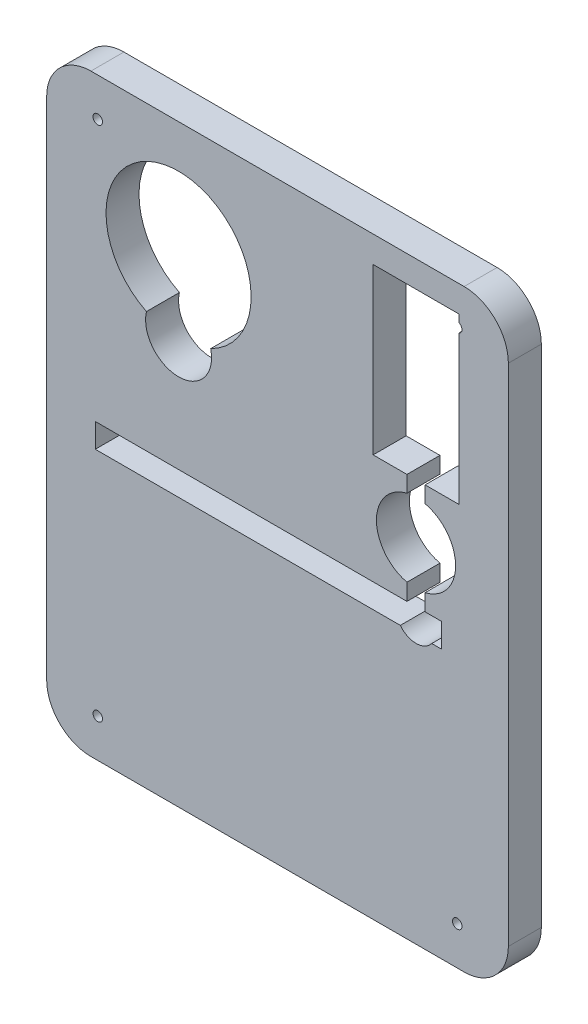
SolidWorks part; units mm, degrees
material "Polyurethane Foam Flexible"
ref_plane "Front Plane" through (0, 0, 0) normal (1, 0, 0) x (0, 1, 0)
ref_plane "Top Plane" through (0, 0, 0) normal (0, 0, 1) x (0, 1, 0)
ref_plane "Right Plane" through (0, 0, 0) normal (0, 1, 0) x (-1, 0, 0)
sketch "Sketch1" plane through (0, 0, 0) normal (0, 0, 1) x (0, 1, 0)
  line L5 (-97.2566, -88.9) -> (97.2566, -88.9)
  line L6 (-114.3, -71.8566) -> (-114.3, 71.8566)
  line L7 (-97.2566, 88.9) -> (97.2566, 88.9)
  line L8 (114.3, -71.8566) -> (114.3, 71.8566)
  arc A0 (-114.3, 71.8566) -> (-97.2566, 88.9) centre (-97.2566, 71.8566) cw
  arc A1 (-97.2566, -88.9) -> (-114.3, -71.8566) centre (-97.2566, -71.8566) cw
  arc A2 (97.2566, -88.9) -> (114.3, -71.8566) centre (97.2566, -71.8566) ccw
  arc A3 (97.2566, 88.9) -> (114.3, 71.8566) centre (97.2566, 71.8566) cw
  point P15 (114.3, 0)
  point P20 (0, 88.9)
  dimension "D1" = 17.0434
  dimension "D2" = 177.8
  dimension "D3" = 228.6
extrude "Boss-Extrude1" add sketch "Sketch1" along normal blind 12.7
sketch "Sketch2" plane through (0, 0, 12.7) normal (0, 0, 1) x (1, 0, 0)
  line L0 (0, 223.1681) -> (0, -217.0396) construction
  line L1 (-162.9401, 0) -> (143.5585, 0) construction
  point P11 (-69.2191, -99.5086)
  point P12 (69.2191, -99.5086)
  point P13 (69.2191, 99.5086)
  point P14 (-69.2191, 99.5086)
  dimension "D1" = 99.5086
  dimension "D2" = 69.2191
  dimension "D3" = 69.2191
  dimension "D4" = 99.5086
  dimension "D5" = 69.2191
  dimension "D6" = 99.5086
  dimension "D7" = 69.2191
  dimension "D8" = 99.5086
sketch "Sketch6" plane through (0, 0, 12.7) normal (0, 0, 1) x (1, 0, 0)
  line L0 (53.34, 139.097) -> (53.34, -37.7787) construction
  line L3 (-38.1, 127.2984) -> (-38.1, 26.2104) construction
  line L4 (49.8475, 4.6918) -> (49.8475, -1.7145)
  line L20 (-114.4724, 69.85) -> (19.4395, 69.85) construction
  line L21 (-38.1, 69.85) -> (-38.1, 107.4547) construction
  line L22 (-162.9401, 0) -> (143.5585, 0) construction
  line L23 (56.8325, 4.6918) -> (56.8325, -1.7145)
  line L25 (117.4238, 79.5655) -> (-13.9103, 79.5655) construction
  line L28 (49.8475, 40.64) -> (49.8475, 34.3607)
  line L35 (56.8325, 40.64) -> (56.8325, 34.3607)
  line L49 (0, 223.1681) -> (0, -217.0396) construction
  line L51 (36.83, 104.14) -> (69.85, 104.14)
  line L52 (36.83, 104.14) -> (36.83, 40.64)
  line L53 (36.83, 40.64) -> (49.8475, 40.64)
  line L54 (69.85, 104.14) -> (69.85, 40.64)
  line L56 (56.8325, 40.64) -> (69.85, 40.64)
  line L60 (82.8638, -6.35) -> (-86.4031, -6.35) construction
  line L61 (63.1825, -10.9855) -> (59.3879, -10.9855)
  line L62 (-70.1675, -10.9855) -> (-70.1675, -1.7145)
  line L63 (-70.1675, -1.7145) -> (49.8475, -1.7145)
  line L64 (56.8325, -1.7145) -> (63.1825, -1.7145)
  line L65 (63.1825, -1.7145) -> (63.1825, -10.9855)
  line L66 (47.2921, -10.9855) -> (-70.1675, -10.9855)
  arc A16 (-25.7323, 44.7964) -> (-50.4677, 44.7964) centre (-38.1, 69.85) ccw
  arc A17 (-50.4677, 44.7964) -> (-25.7323, 44.7964) centre (-38.1, 41.91) ccw
  arc A18 (56.8325, 4.6918) -> (56.8325, 34.3607) centre (53.34, 19.5262) ccw
  arc A19 (49.8475, 34.3607) -> (49.8475, 4.6918) centre (53.34, 19.5262) ccw
  arc A20 (47.2921, -10.9855) -> (59.3879, -10.9855) centre (53.34, -6.35) ccw
  dimension "D12" = 55.88
  dimension "D13" = 25.4
  dimension "D6" = 30.48
  dimension "D22" = 15.24
  dimension "D11" = 69.85
  dimension "D14" = 38.1
  dimension "D3" = 53.34
  dimension "D5" = 79.5655
  dimension "D15" = 63.5
  dimension "D16" = 33.02
  dimension "D17" = 40.64
  dimension "D18" = 16.51
  dimension "D7" = 3.4925
  dimension "D8" = 3.4925
  dimension "D19" = 21.1137
  dimension "D20" = 46.99
  dimension "D4" = 4.6355
  dimension "D10" = 4.6355
  dimension "D9" = 6.35
  dimension "D21" = 133.35
extrude "Cut-Extrude1" cut sketch "Sketch6" against normal through all
hole_wizard "#27 (0.144) Diameter Hole1" positions "Sketch2" profile "Sketch7" hole size "#27" standard "ANSI Inch" end condition through all
sketch "Sketch7" plane through (-69.2191, 99.5086, 12.7) normal (1, 0, 0) x (0, -1, 0)
  line L0 (0, 0) -> (0, 12.7)
  line L1 (0, 12.7) -> (1.8288, 12.7)
  line L2 (1.8288, 12.7) -> (1.8288, 0)
  line L5 (1.8288, 0) -> (0, 0)
  line L11 (0, -6.35) -> (0, 107.95) construction
  dimension "Thru Hole Dia." = 3.6576
  dimension "Thru Hole Depth" = 12.7
equation "\"D8@Sketch6\"=\"D7@Sketch6\""
equation "\"D10@Sketch6\"=\"D4@Sketch6\""
equation "\"D3@Sketch2\"=\"D2@Sketch2\""
equation "\"D4@Sketch2\"=\"D1@Sketch2\""
equation "\"D5@Sketch2\"=\"D2@Sketch2\""
equation "\"D6@Sketch2\"=\"D1@Sketch2\""
equation "\"D7@Sketch2\"=\"D2@Sketch2\""
equation "\"D8@Sketch2\"=\"D1@Sketch2\""
